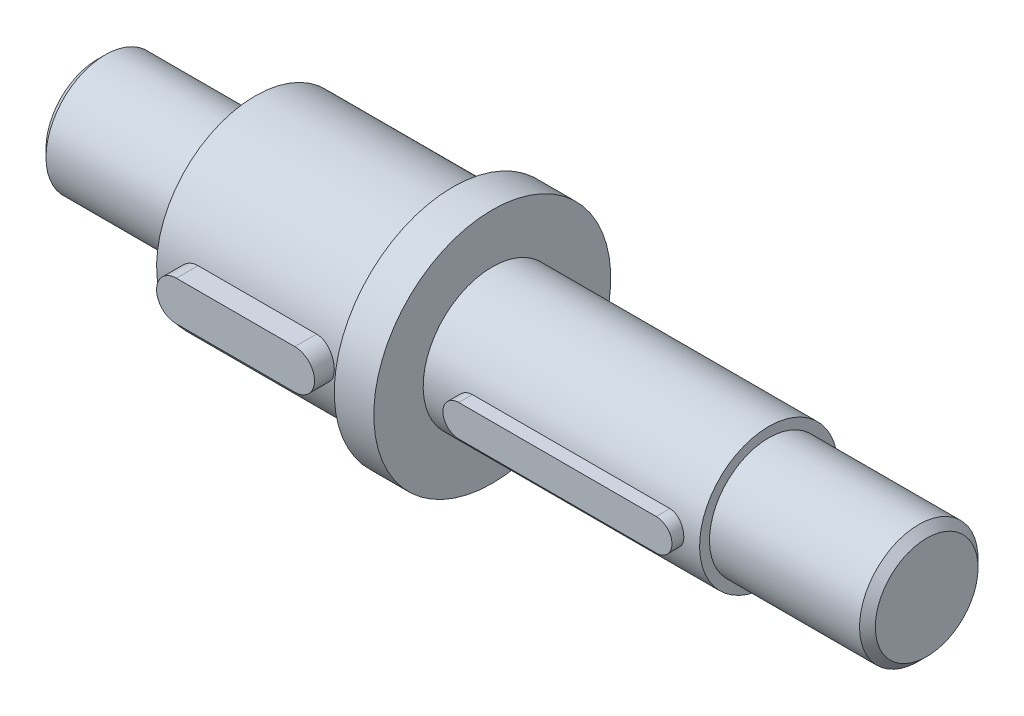
SolidWorks part; units mm, degrees
ref_plane "Front Plane" through (0, 0, 0) normal (0, 0, 1) x (1, 0, 0)
ref_plane "Top Plane" through (0, 0, 0) normal (0, 1, 0) x (1, 0, 0)
ref_plane "Right Plane" through (0, 0, 0) normal (1, 0, 0) x (0, 0, -1)
sketch "Sketch1" plane through (0, 0, 0) normal (0, 0, 1) x (1, 0, 0)
  line L0 (0, 0) -> (0, 15)
  line L1 (0, 15) -> (40, 15)
  line L2 (40, 15) -> (40, 25)
  line L3 (40, 25) -> (90, 25)
  line L4 (90, 25) -> (90, 30)
  line L5 (90, 30) -> (100, 30)
  line L6 (100, 30) -> (100, 17.5)
  line L7 (100, 17.5) -> (170, 17.5)
  line L8 (170, 17.5) -> (170, 15)
  line L9 (170, 15) -> (210, 15)
  line L10 (210, 15) -> (210, 0)
  line L11 (210, 0) -> (0, 0)
  dimension "D1" = 40
  dimension "D2" = 50
  dimension "D3" = 10
  dimension "D4" = 70
  dimension "D5" = 40
  dimension "D6" = 15
  dimension "D7" = 25
  dimension "D8" = 30
  dimension "D9" = 17.5
  dimension "D10" = 15
revolve "Revolve1" add sketch "Sketch1" angle 360 about L11
ref_plane "Plane1" through (0, 0, 17.5) normal (0, 0, 1) x (1, 0, 0)
sketch "Sketch2" plane through (0, 0, 17.5) normal (0, 0, 1) x (1, 0, 0)
  line L1 (0, 0) -> (232.3443, 0) construction
  line L3 (112, -4) -> (162, -4)
  line L5 (112, 4) -> (162, 4)
  line L7 (112, -4) -> (162, 4) construction
  line L8 (112, 4) -> (162, -4) construction
  arc A0 (162, -4) -> (162, 4) centre (162, 0) ccw
  arc A1 (112, 4) -> (112, -4) centre (112, 0) ccw
  point P1 (137, 0)
  dimension "D1" = 8
  dimension "D2" = 50
ref_plane "Plane2" through (0, 0, 25) normal (0, 0, 1) x (1, 0, 0)
chamfer "Chamfer1" distance 2 angle 45 1 edges at (0, 15, 0)
chamfer "Chamfer2" distance 2 angle 45 1 edges at (210, 15, 0)
sketch "Sketch8" plane through (0, 0, 25) normal (0, 0, 1) x (1, 0, 0)
  line L0 (0, 0) -> (-50.9793, 0) construction
  line L2 (50, -5) -> (80, -5)
  line L4 (50, 5) -> (80, 5)
  line L6 (50, -5) -> (80, 5) construction
  line L7 (50, 5) -> (80, -5) construction
  arc A1 (80, -5) -> (80, 5) centre (80, 0) ccw
  arc A2 (50, 5) -> (50, -5) centre (50, 0) ccw
  point P1 (65, 0)
  dimension "D5" = 10
  dimension "D1" = 30
  dimension "D2" = 10
extrude "Cut-Extrude1" cut sketch "Sketch2" against normal blind 3 contours L3 A0 L5 A1
extrude "Cut-Extrude2" cut sketch "Sketch8" against normal blind 5 contours L4 A1 L2 A2
sketch "Sketch11" plane through (0, 0, 14.5) normal (0, 0, 1) x (1, 0, 0)
  line L2 (112, -4) -> (162, -4)
  line L3 (162, 4) -> (112, 4)
  line L4 (112, -4) -> (162, -4)
  line L5 (162, 4) -> (112, 4)
  arc A2 (112, 4) -> (112, -4) centre (112, 0) ccw
  arc A3 (162, -4) -> (162, 4) centre (162, 0) ccw
  arc A4 (112, 4) -> (112, -4) centre (112, 0) ccw
  arc A5 (162, -4) -> (162, 4) centre (162, 0) ccw
  dimension "D1" = 0
sketch "Sketch12" plane through (0, 0, 20) normal (0, 0, 1) x (1, 0, 0)
  line L2 (50, -5) -> (80, -5)
  line L3 (80, 5) -> (50, 5)
  line L4 (50, -5) -> (80, -5)
  line L5 (80, 5) -> (50, 5)
  arc A2 (50, 5) -> (50, -5) centre (50, 0) ccw
  arc A3 (80, -5) -> (80, 5) centre (80, 0) ccw
  arc A4 (50, 5) -> (50, -5) centre (50, 0) ccw
  arc A5 (80, -5) -> (80, 5) centre (80, 0) ccw
  dimension "D1" = 0
extrude "Boss-Extrude2" add sketch "Sketch11" along normal blind 6 separate body contours L4 A5 L5 A4
extrude "Boss-Extrude3" add sketch "Sketch12" along normal blind 10 contours L4 A5 L5 A4
